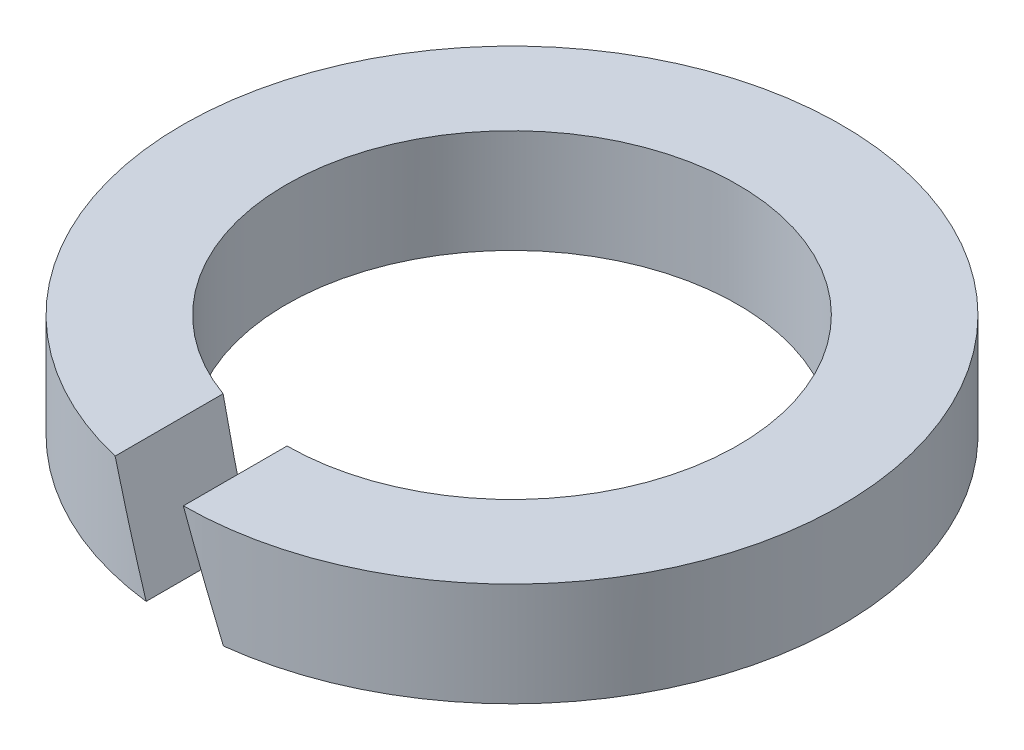
SolidWorks part; units mm, degrees
ref_plane "Спереди" through (0, 0, 0) normal (0, 0, 1) x (1, 0, 0)
ref_plane "Сверху" through (0, 0, 0) normal (0, 1, 0) x (1, 0, 0)
ref_plane "Справа" through (0, 0, 0) normal (1, 0, 0) x (0, 0, -1)
sketch "Ske" plane through (0, 0, 0) normal (0, 0, 1) x (1, 0, 0)
  line L0 (0, 15.7597) -> (0, -13.7032) construction
  line L1 (-3.05, 0) -> (-4.45, 0)
  line L2 (-3.05, 0) -> (-3.05, 1.4)
  line L3 (-3.05, 1.4) -> (-4.45, 1.4)
  line L4 (-4.45, 0) -> (-4.45, 1.4)
  dimension "S" = 1.4
  dimension "H" = 1.4
  dimension "Insid_Dia" = 6.1
revolve "Base" add sketch "Ske" angle 360 about L0
sketch "Ske4" plane through (0, 0, 0) normal (0, 0, 1) x (1, 0, 0)
  line L0 (0, 0) -> (-0.6869, 1.8873) construction
  line L1 (-3.05, 0) -> (3.05, 0) construction
  line L2 (3.05, 1.4) -> (-3.05, 1.4) construction
  line L3 (-0.5214, 0) -> (0.5214, 0)
  line L4 (0.0119, 1.4) -> (-1.031, 1.4)
  line L5 (0.0119, 1.4) -> (0.5214, 0)
  line L6 (-1.031, 1.4) -> (-0.5214, 0)
  dimension "D1" = 110
  dimension "D2" = 0.98
extrude "Cut" cut sketch "Ske4" along normal up to next
equation "\"D2@Ske4\"=0.7*\"H@Ske\""
